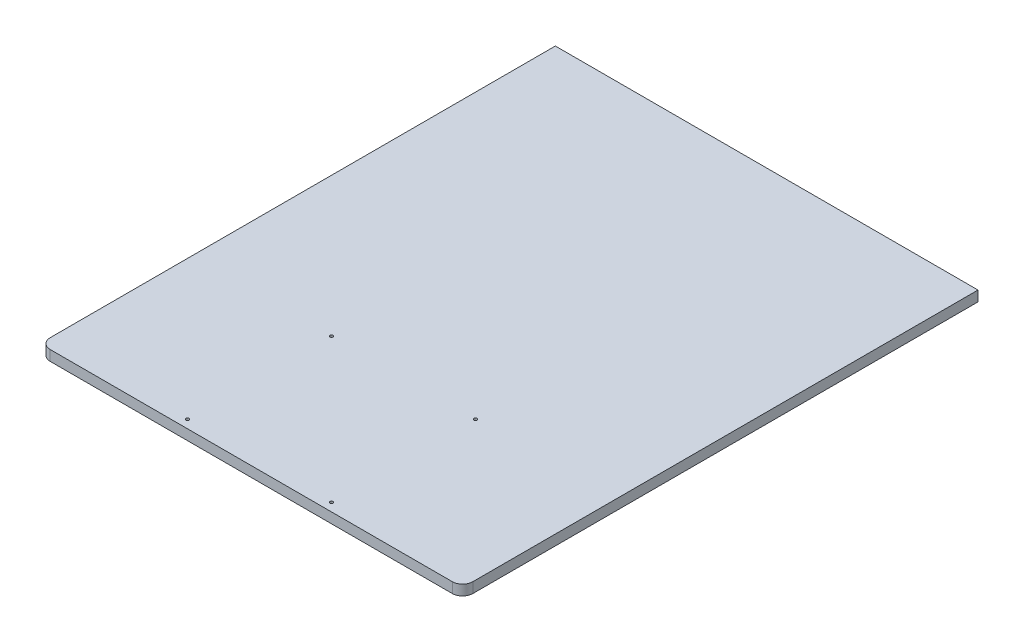
SolidWorks part; units mm, degrees
ref_plane "Front Plane" through (0, 0, 0) normal (0, 0, 1) x (1, 0, 0)
ref_plane "Top Plane" through (0, 0, 0) normal (0, 1, 0) x (1, 0, 0)
ref_plane "Right Plane" through (0, 0, 0) normal (1, 0, 0) x (0, 0, -1)
sketch "Sketch1" plane through (0, 0, 0) normal (0, 1, 0) x (1, 0, 0)
  line L1 (-205, 250) -> (205, 250)
  line L2 (-205, 250) -> (-205, -250)
  line L3 (-205, -250) -> (205, -250)
  line L4 (205, 250) -> (205, -250)
  line L5 (0, -250) -> (0, 250) construction
  line L6 (-205, 0) -> (205, 0) construction
  line L9 (-77.8514, -250) -> (77.8514, -250)
  line L10 (0, -94.2972) -> (0, -250) construction
  circle A0 centre (-69.8514, -242) radius 1.5
  circle A1 centre (-69.8514, -102.2972) radius 1.5
  circle A2 centre (69.8514, -102.2972) radius 1.5
  circle A3 centre (69.8514, -242) radius 1.5
  point P0 (0, 0)
  point P14 (0, -250)
  dimension "D1" = 500
  dimension "D2" = 410
extrude "Boss-Extrude1" add sketch "Sketch1" along normal blind 10 contours L4 L1 L2 L3 A0 A1 A2 A3
fillet "Fillet1" radius 10 2 edges at (-205, 5, 250) (205, 5, 250)
